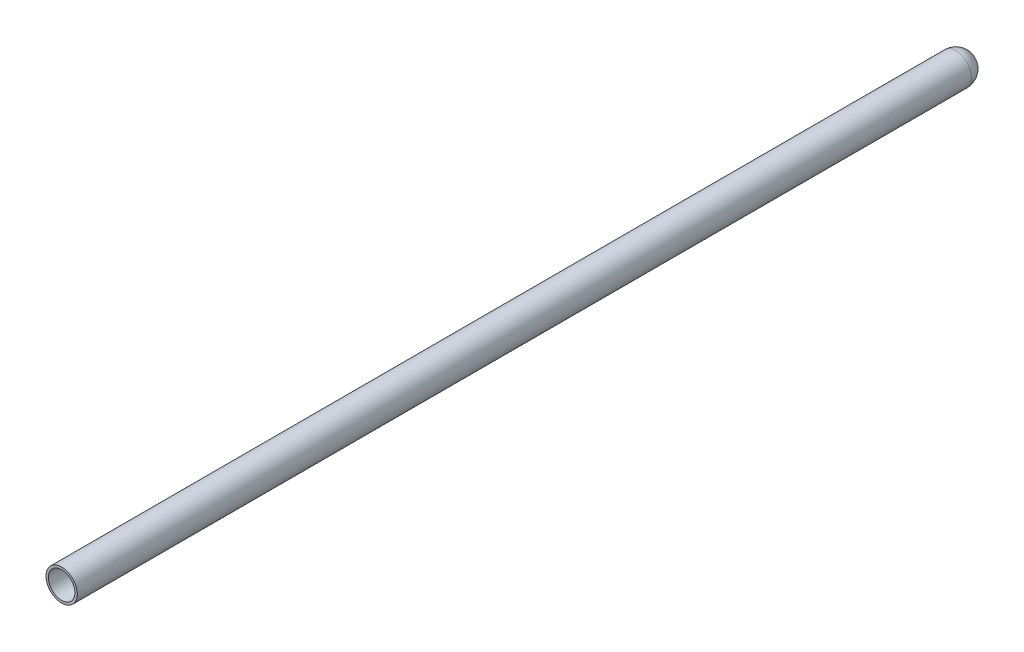
SolidWorks part; units mm, degrees
ref_plane "Front Plane" through (0, 0, 0) normal (0, 0, 1) x (1, 0, 0)
ref_plane "Top Plane" through (0, 0, 0) normal (0, 1, 0) x (1, 0, 0)
ref_plane "Right Plane" through (0, 0, 0) normal (1, 0, 0) x (0, 0, -1)
other "Graphic1"
sketch "Sketch2" plane through (0, 0, 0) normal (0, 1, 0) x (1, 0, 0)
  line L0 (2.2, -84.6) -> (2.2, 63.8)
  line L1 (0, 0) -> (0, 1.0185) construction
  line L2 (2.6, -84.6) -> (2.6, 63.8)
  line L3 (2.2, -84.6) -> (2.6, -84.6)
  line L4 (0, 66.4) -> (0, 66)
  arc A0 (2.2, 63.8) -> (0, 66) centre (0, 63.8) ccw
  arc A1 (2.6, 63.8) -> (0, 66.4) centre (0, 63.8) ccw
  dimension "D1" = 2.2
  dimension "D2" = 84.6
  dimension "D3" = 66
  dimension "D4" = 0.4
revolve "Revolve1" add sketch "Sketch2" angle 360 about L1
